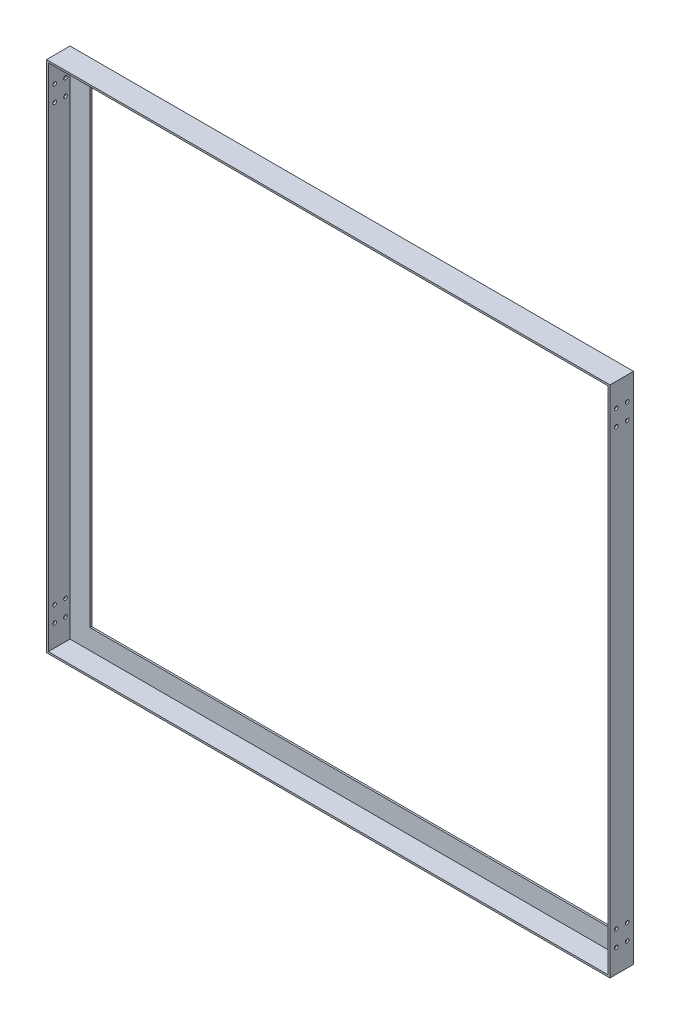
SolidWorks part; units mm, degrees
material "Acero al carbono no aleado"
ref_plane "Alzado" through (0, 0, 0) normal (0, 0, 1) x (1, 0, 0)
ref_plane "Planta" through (0, 0, 0) normal (0, 1, 0) x (1, 0, 0)
ref_plane "Vista lateral" through (0, 0, 0) normal (1, 0, 0) x (0, 0, -1)
sketch "Croquis1" plane through (0, 0, 0) normal (0, 0, 1) x (1, 0, 0)
  line L1 (0, 0) -> (-987.3, 0)
  line L2 (0, 0) -> (0, 900)
  line L3 (0, 900) -> (-987.3, 900)
  line L4 (-987.3, 0) -> (-987.3, 900)
  line L5 (-38.1, 38.1) -> (-949.2, 38.1)
  line L6 (-38.1, 38.1) -> (-38.1, 861.9)
  line L7 (-38.1, 861.9) -> (-949.2, 861.9)
  line L8 (-949.2, 38.1) -> (-949.2, 861.9)
  dimension "D1" = 38.1
  dimension "D2" = 38.1
  dimension "D3" = 38.1
  dimension "D4" = 38.1
  dimension "D5" = 987.3
  dimension "D6" = 900
extrude "Saliente-Extruir1" add sketch "Croquis1" along normal blind 3.1
sketch "Croquis2" plane through (0, 0, 3.1) normal (0, 0, 1) x (1, 0, 0)
  line L0 (0, 900) -> (-987.3, 900) construction
  line L1 (-987.3, 900) -> (0, 900)
  line L2 (-987.3, 900) -> (-987.3, 0)
  line L3 (-987.3, 0) -> (0, 0)
  line L4 (0, 900) -> (0, 0)
  line L5 (-984.2, 896.9) -> (-3.1, 896.9)
  line L6 (-984.2, 896.9) -> (-984.2, 3.1)
  line L7 (-984.2, 3.1) -> (-3.1, 3.1)
  line L8 (-3.1, 896.9) -> (-3.1, 3.1)
  dimension "D1" = 3.1
  dimension "D2" = 3.1
  dimension "D3" = 3.1
  dimension "D4" = 3.1
extrude "Saliente-Extruir2" add sketch "Croquis2" along normal blind 38.1
sketch "Croquis3" plane through (-987.3, 0, 0) normal (-1, 0, 0) x (0, 0, 1)
  line L0 (20.6, 900) -> (20.6, 949.1748) construction
  line L3 (41.2, 900) -> (0, 900) construction
  line L4 (11.075, 900) -> (11.075, 946.0875) construction
  line L6 (0, 900) -> (0, 0) construction
  line L7 (41.2, 450) -> (0, 450) construction
  line L8 (41.2, 900) -> (41.2, 0) construction
  circle A2 centre (11.075, 859) radius 3.175
  circle A3 centre (11.075, 831) radius 3.175
  circle A4 centre (30.125, 859) radius 3.175
  circle A5 centre (30.125, 831) radius 3.175
  circle A6 centre (30.125, 69) radius 3.175
  circle A7 centre (11.075, 69) radius 3.175
  circle A8 centre (11.075, 41) radius 3.175
  circle A9 centre (30.125, 41) radius 3.175
  dimension "D3" = 28
  dimension "D1" = 762
  dimension "D2" = 19.05
extrude "Cortar-Extruir1" cut sketch "Croquis3" against normal blind 1000
